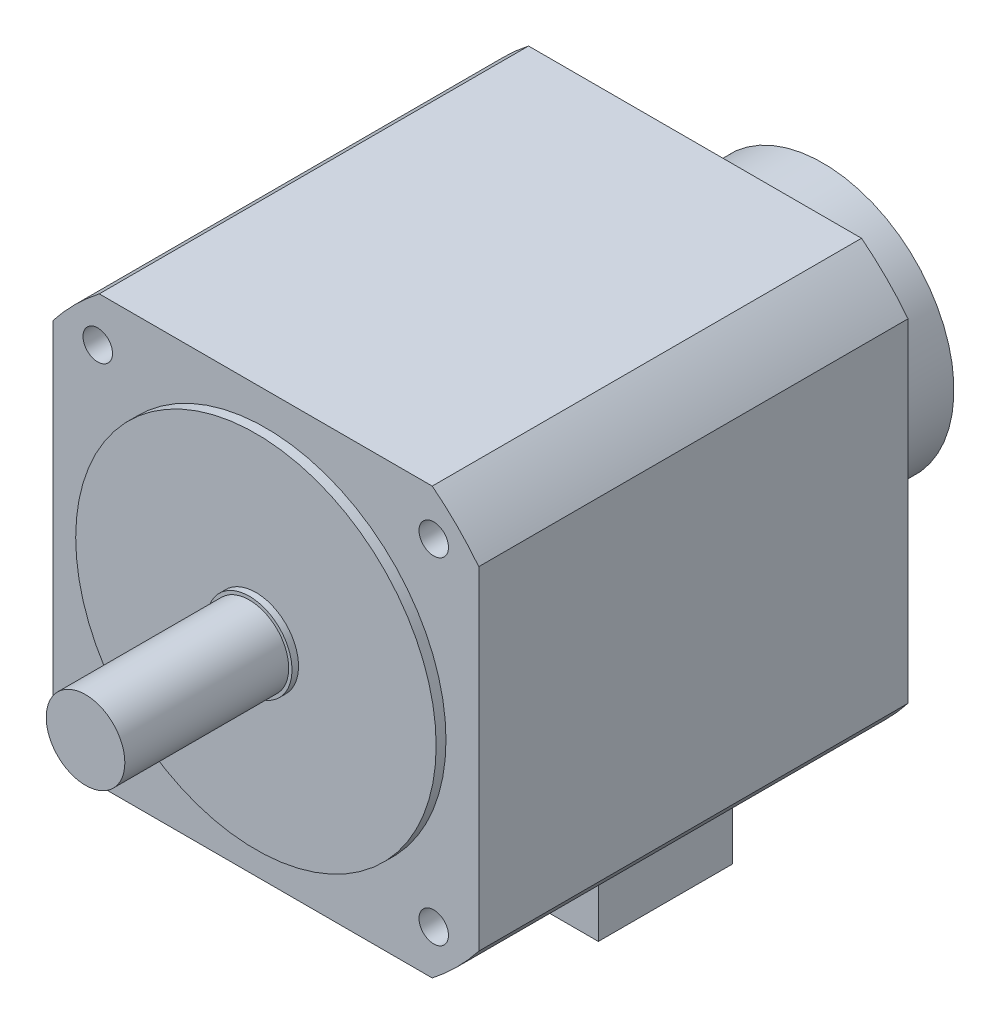
SolidWorks part; units mm, degrees
ref_plane "Front Plane" through (0, 0, 0) normal (0, 0, 1) x (1, 0, 0)
ref_plane "Top Plane" through (0, 0, 0) normal (0, 1, 0) x (1, 0, 0)
ref_plane "Right Plane" through (0, 0, 0) normal (1, 0, 0) x (0, 0, -1)
sketch "Sketch1" plane through (0, 0, 0) normal (0, 0, 1) x (1, 0, 0)
  circle A0 centre (0, 0) radius 12
  dimension "D1" = 24
extrude "Boss-Extrude1" add sketch "Sketch1" against normal blind 50
sketch "Sketch2" plane through (0, 0, -50) normal (0, 0, -1) x (-1, 0, 0)
  circle A0 centre (0, 0) radius 13
  dimension "D1" = 26
extrude "Boss-Extrude2" add sketch "Sketch2" along normal blind 2
sketch "Sketch3" plane through (0, 0, -52) normal (0, 0, -1) x (-1, 0, 0)
  circle A0 centre (0, 0) radius 55
  dimension "D1" = 110
extrude "Boss-Extrude3" add sketch "Sketch3" along normal blind 3
sketch "Sketch4" plane through (0, 0, -55) normal (0, 0, -1) x (-1, 0, 0)
  line L1 (-50.806, -65) -> (50.806, -65)
  line L2 (-65, -50.806) -> (-65, 50.806)
  line L3 (-50.806, 65) -> (50.806, 65)
  line L4 (65, -50.806) -> (65, 50.806)
  line L5 (-65, -65) -> (65, 65) construction
  line L6 (-65, 65) -> (65, -65) construction
  arc A0 (-50.806, 65) -> (-65, 50.806) centre (0, 0) ccw
  arc A1 (-65, -50.806) -> (-50.806, -65) centre (0, 0) ccw
  arc A2 (50.806, -65) -> (65, -50.806) centre (0, 0) ccw
  arc A3 (65, 50.806) -> (50.806, 65) centre (0, 0) ccw
  point P0 (0, 0)
  dimension "D2" = 165
  dimension "D1" = 130
extrude "Boss-Extrude4" add sketch "Sketch4" along normal blind 131
sketch "Sketch5" plane through (0, 0, -186) normal (0, 0, -1) x (-1, 0, 0)
  line L0 (0, 0) -> (0, -65) construction
  line L1 (-50.806, -65) -> (50.806, -65) construction
  line L2 (-19.5, -34.9249) -> (-19.5, -81.5)
  line L3 (19.5, -34.9249) -> (19.5, -81.5)
  line L4 (-19.5, -81.5) -> (19.5, -81.5)
  arc A1 (19.5, -34.9249) -> (-19.5, -34.9249) centre (0, 0) ccw
  dimension "D1" = 80
  dimension "D2" = 81.5
  dimension "D3" = 39
extrude "Boss-Extrude5" add sketch "Sketch5" along normal blind 39
sketch "Sketch6" plane through (0, 0, -55) normal (0, 0, 1) x (1, 0, 0)
  line L0 (0, 0) -> (-58.3363, 58.3363) construction
  arc A0 (-50.806, 65) -> (-65, 50.806) centre (0, 0) ccw construction
  circle A1 centre (-51.2652, 51.2652) radius 4.5
  circle A2 centre (51.2652, 51.2652) radius 4.5
  circle A3 centre (51.2652, -51.2652) radius 4.5
  circle A4 centre (-51.2652, -51.2652) radius 4.5
  point P17 (0, 0)
  dimension "D1" = 9
  dimension "D2" = 72.5
  dimension "D3" = 4
extrude "Cut-Extrude1" cut sketch "Sketch6" against normal blind 15
sketch "Sketch7" plane through (0, -65, 0) normal (0, -1, 0) x (1, 0, 0)
  line L0 (0, 0) -> (0, -234.2061) construction
  line L1 (65, -55) -> (50.806, -55) construction
  line L2 (-20.5, -177) -> (20.5, -177)
  line L3 (-20.5, -177) -> (-20.5, -136)
  line L4 (-20.5, -136) -> (20.5, -136)
  line L5 (20.5, -177) -> (20.5, -136)
  line L6 (-20.5, -177) -> (20.5, -136) construction
  line L7 (-20.5, -136) -> (20.5, -177) construction
  point P3 (0, -156.5)
  dimension "D1" = 41
  dimension "D2" = 101.5
extrude "Boss-Extrude6" add sketch "Sketch7" along normal blind 46
